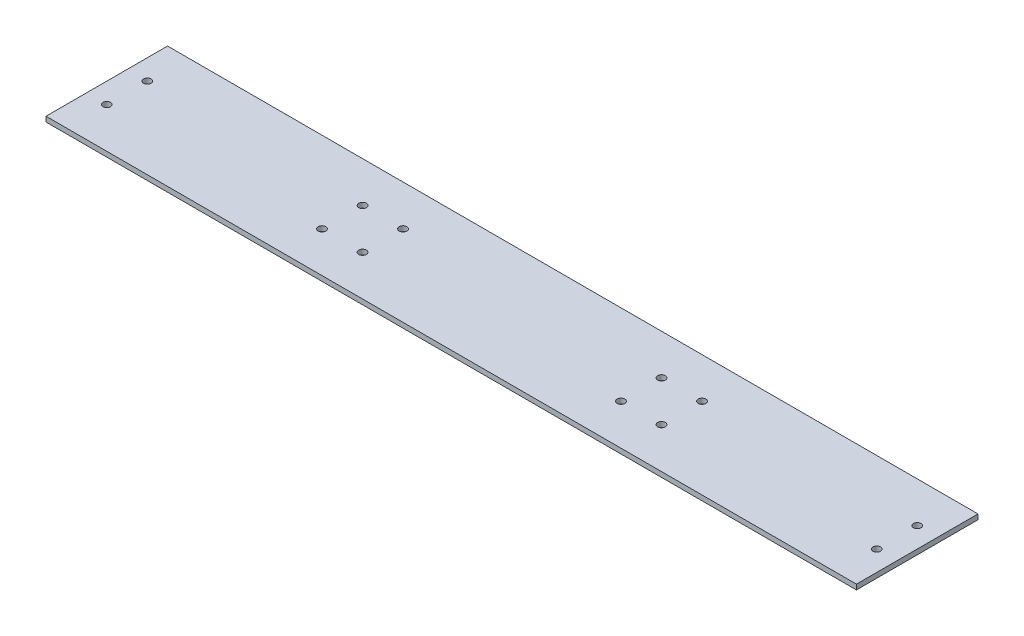
SolidWorks part; units mm, degrees
material "6061 Alloy"
ref_plane "Front Plane" through (0, 0, 0) normal (0, 0, 1) x (1, 0, 0)
ref_plane "Top Plane" through (0, 0, 0) normal (0, 1, 0) x (1, 0, 0)
ref_plane "Right Plane" through (0, 0, 0) normal (1, 0, 0) x (0, 0, -1)
sketch "Sketch1" plane through (0, 0, 0) normal (0, 1, 0) x (1, 0, 0)
  line L1 (254, -38.1) -> (-254, -38.1)
  line L2 (254, -38.1) -> (254, 38.1)
  line L3 (254, 38.1) -> (-254, 38.1)
  line L4 (-254, -38.1) -> (-254, 38.1)
  line L5 (254, -38.1) -> (-254, 38.1) construction
  line L6 (254, 38.1) -> (-254, -38.1) construction
  point P0 (0, 0)
  dimension "D1" = 508
  dimension "D2" = 76.2
extrude "Boss-Extrude1" add sketch "Sketch1" along normal blind 3.175
sketch "Sketch2" plane through (0, 3.175, 0) normal (0, 1, 0) x (1, 0, 0)
  circle A0 centre (-106.3399, -12.7385) radius 2.413
  circle A1 centre (-106.3399, 12.6615) radius 2.413
  circle A2 centre (-80.9399, 12.6615) radius 2.413
  circle A3 centre (-80.9399, -12.7385) radius 2.413
  circle A4 centre (106.3387, -12.6204) radius 2.413
  circle A5 centre (106.3387, 12.7796) radius 2.413
  circle A6 centre (80.9387, 12.7796) radius 2.413
  circle A7 centre (80.9387, -12.6204) radius 2.413
extrude "Cut-Extrude1" cut sketch "Sketch2" against normal blind 3.175
sketch "Sketch3" plane through (0, 3.175, 0) normal (0, 1, 0) x (1, 0, 0)
  line L1 (-241.3, 38.1) -> (-241.3, 12.7) construction
  line L2 (254, 38.1) -> (-254, 38.1) construction
  line L3 (-241.3, 12.7) -> (-241.3, -12.7) construction
  line L4 (-241.3, -12.7) -> (-241.3, -38.1) construction
  line L5 (-254, -38.1) -> (254, -38.1) construction
  line L6 (-254, 38.1) -> (-254, -38.1) construction
  line L7 (-254, 38.1) -> (254, 38.1) construction
  line L8 (0, 38.1) -> (0, -38.1) construction
  line L9 (241.3, -12.7) -> (241.3, -38.1) construction
  line L10 (241.3, 12.7) -> (241.3, -12.7) construction
  line L11 (241.3, 38.1) -> (241.3, 12.7) construction
  circle A0 centre (-241.3, 12.7) radius 2.3813
  circle A1 centre (-241.3, -12.7) radius 2.3813
  circle A2 centre (241.3, -12.7) radius 2.3813
  circle A3 centre (241.3, 12.7) radius 2.3813
  dimension "D2" = 25.4
  dimension "D3" = 4.7625
  dimension "D1" = 12.7
extrude "Cut-Extrude2" cut sketch "Sketch3" against normal blind 3.175
